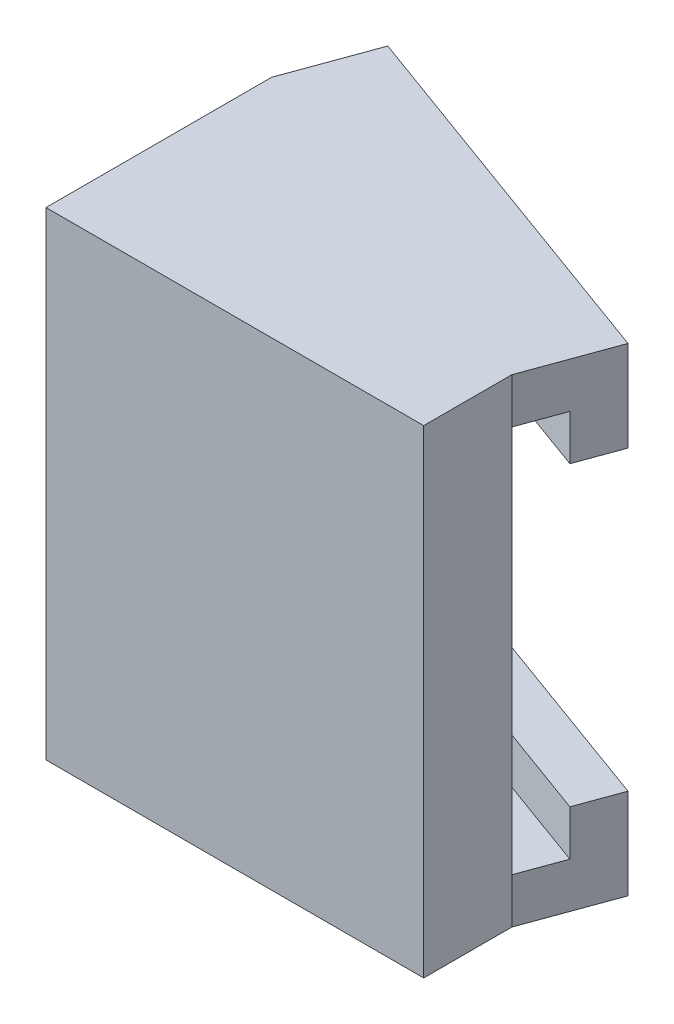
SolidWorks part; units mm, degrees
ref_plane "Ebene vorne" through (0, 0, 0) normal (0, 0, 1) x (1, 0, 0)
ref_plane "Ebene oben" through (0, 0, 0) normal (0, 1, 0) x (1, 0, 0)
ref_plane "Ebene rechts" through (0, 0, 0) normal (1, 0, 0) x (0, 0, -1)
sketch "Skizze1" plane through (0, 0, 0) normal (0, 0, 1) x (1, 0, 0)
  line L1 (-7.5, -9.5) -> (7.5, -9.5)
  line L2 (-7.5, -9.5) -> (-7.5, 9.5)
  line L3 (-7.5, 9.5) -> (7.5, 9.5)
  line L4 (7.5, -9.5) -> (7.5, 9.5)
  line L5 (-7.5, -9.5) -> (7.5, 9.5) construction
  line L6 (-7.5, 9.5) -> (7.5, -9.5) construction
  point P0 (0, 0)
  dimension "D1" = 15
  dimension "D2" = 19
extrude "Aufsatz-Linear austragen1" add sketch "Skizze1" along normal blind 3
sketch "Skizze3" plane through (0, 9.5, 0) normal (0, 1, 0) x (1, 0, 0)
  line L0 (-7.5, 0) -> (-7.5, 5.4596)
  line L1 (-7.5, 5.4596) -> (7.5, 0)
  line L2 (7.5, 0) -> (-7.5, 0) construction
  line L3 (-7.5, 0) -> (7.5, 0)
  dimension "D1" = 20
extrude "Aufsatz-Linear austragen2" add sketch "Skizze3" against normal blind 19
sketch "Skizze5" plane through (0, 0, 3) normal (0, 0, 1) x (1, 0, 0)
  circle A0 centre (0, 0) radius 3
  dimension "D1" = 6
extrude "Schnitt-Linear austragen1" cut sketch "Skizze5" against normal blind 3
sketch "Skizze6" plane through (0, 0, 3) normal (0, 0, 1) x (1, 0, 0)
  line L4 (7.5, -9.5) -> (7.5, 9.5)
  line L5 (7.5, 9.5) -> (-7.5, 9.5)
  line L6 (-7.5, 9.5) -> (-7.5, -9.5)
  line L7 (-7.5, -9.5) -> (7.5, -9.5)
  line L8 (7.5, -9.5) -> (7.5, 9.5)
  line L9 (7.5, 9.5) -> (-7.5, 9.5)
  line L10 (-7.5, 9.5) -> (-7.5, -9.5)
  line L11 (-7.5, -9.5) -> (7.5, -9.5)
  dimension "D1" = 0
extrude "Aufsatz-Linear austragen3" add sketch "Skizze6" along normal blind 0.5
sketch "Skizze7" plane through (0.8773, 0, -2.4105) normal (0.342, 0, -0.9397) x (-0.9397, 0, -0.342)
  line L0 (-7.0477, -9.5) -> (-7.0477, 9.5) construction
  line L1 (8.915, 9.5) -> (-7.0477, 9.5)
  line L2 (8.915, 9.5) -> (8.915, 7.7)
  line L3 (8.915, 7.7) -> (-7.0477, 7.7)
  line L4 (-7.0477, 9.5) -> (-7.0477, 7.7)
  line L5 (8.915, -9.5) -> (8.915, 9.5) construction
  line L6 (-7.0477, -9.5) -> (8.915, -9.5)
  line L7 (-7.0477, -9.5) -> (-7.0477, -7.7)
  line L8 (-7.0477, -7.7) -> (8.915, -7.7)
  line L9 (8.915, -9.5) -> (8.915, -7.7)
  dimension "D1" = 1.8
  dimension "D2" = 1.8
extrude "Aufsatz-Linear austragen4" add sketch "Skizze7" along normal blind 3.6
sketch "Skizze9" plane through (0, -7.7, 0) normal (0, 1, 0) x (1, 0, 0)
  line L0 (8.1156, 1.6914) -> (-6.8844, 7.151)
  line L1 (8.7313, 3.3829) -> (7.5, 0) construction
  line L2 (-6.2687, 8.8424) -> (-7.5, 5.4596) construction
  line L3 (-6.8844, 7.151) -> (-6.2687, 8.8424)
  line L4 (-6.2687, 8.8424) -> (8.7313, 3.3829)
  line L5 (8.7313, 3.3829) -> (8.1156, 1.6914)
  dimension "D1" = 1.8
sketch "Skizze10" plane through (0, 7.7, 0) normal (0, -1, 0) x (1, 0, 0)
  line L0 (8.7313, -3.3829) -> (8.1156, -1.6914)
  line L1 (8.7313, -3.3829) -> (7.5, 0) construction
  line L2 (8.1156, -1.6914) -> (-6.8844, -7.151)
  line L3 (-6.2687, -8.8424) -> (-7.5, -5.4596) construction
  line L4 (-6.8844, -7.151) -> (-6.2687, -8.8424)
  line L5 (-6.2687, -8.8424) -> (8.7313, -3.3829)
extrude "Aufsatz-Linear austragen5" add sketch "Skizze10" along normal blind 1.8
extrude "Aufsatz-Linear austragen6" add sketch "Skizze9" along normal blind 1.8
